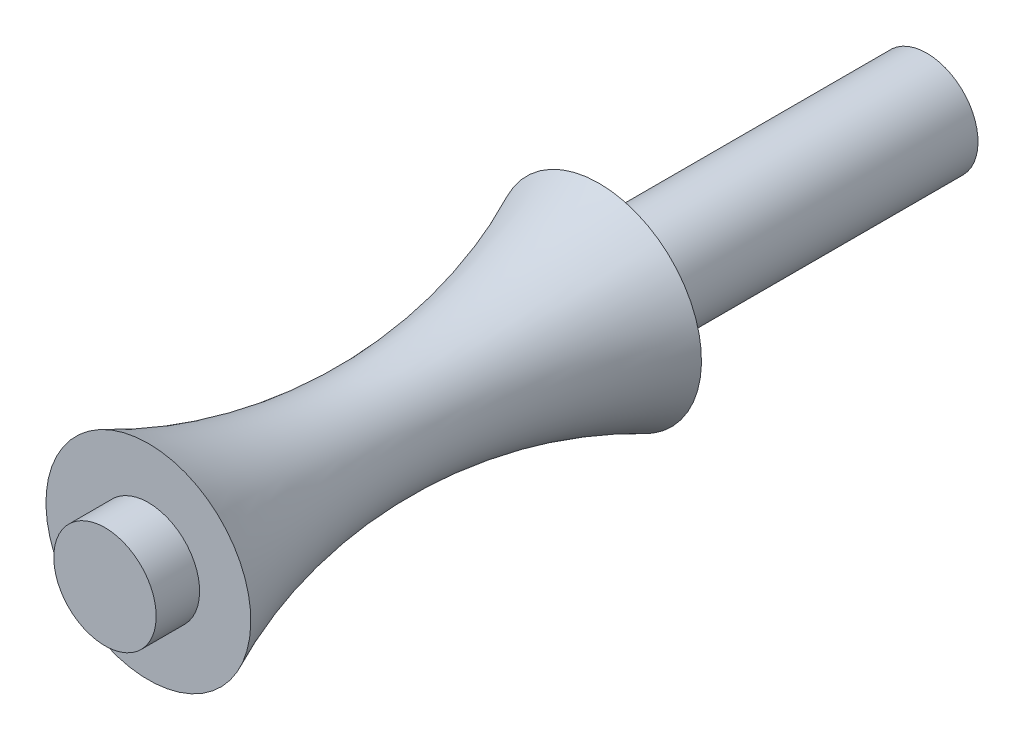
SolidWorks part; units mm, degrees
material "Stop 6061"
ref_plane "Płaszczyzna XY" through (0, 0, 0) normal (0, 0, 1) x (1, 0, 0)
ref_plane "Płaszczyzna XZ" through (0, 0, 0) normal (0, 1, 0) x (1, 0, 0)
ref_plane "Płaszczyzna YZ" through (0, 0, 0) normal (1, 0, 0) x (0, 0, -1)
sketch "Szkic1" plane through (0, 0, 0) normal (1, 0, 0) x (0, 0, -1)
  line L0 (24.6873, -1.7482) -> (-13.3127, -1.7482)
  line L1 (-13.3127, 0.7518) -> (-13.3127, 3.2518)
  line L2 (24.6873, -1.7482) -> (24.6873, 0.7518)
  line L3 (8.6873, 0.7518) -> (8.6873, 3.2518)
  line L4 (24.6873, 0.7518) -> (8.6873, 0.7518)
  line L5 (-13.3127, -1.7482) -> (-15.4312, -1.7482)
  line L6 (-15.4312, -1.7482) -> (-15.4312, 0.7518)
  line L7 (-15.4312, 0.7518) -> (-13.3127, 0.7518)
  arc A1 (-13.3127, 3.2518) -> (8.6873, 3.2518) centre (-2.3127, 26.8532) ccw
  dimension "D1" = 2.5
  dimension "D2" = 5
  dimension "D3" = 22
  dimension "D4" = 16
  dimension "D5" = 2.5
  dimension "D6" = 2.5
revolve "Obrót1" add sketch "Szkic1" angle 360 about L0
